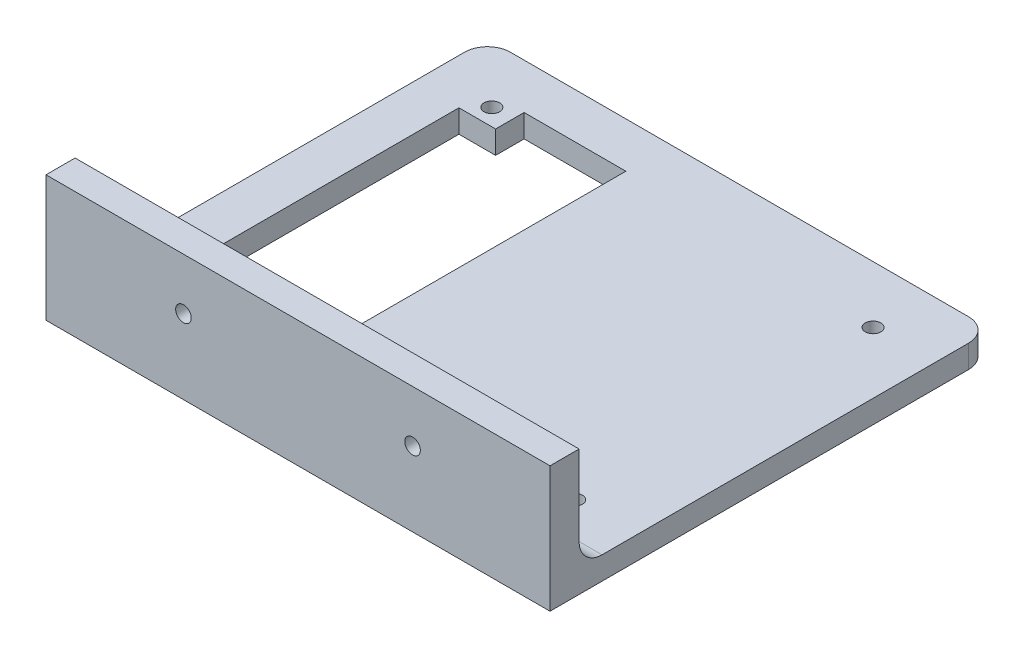
SolidWorks part; units mm, degrees
ref_plane "Front Plane" through (0, 0, 0) normal (0, 0, 1) x (1, 0, 0)
ref_plane "Top Plane" through (0, 0, 0) normal (0, 1, 0) x (1, 0, 0)
ref_plane "Right Plane" through (0, 0, 0) normal (1, 0, 0) x (0, 0, -1)
sketch "Sketch1" plane through (0, 0, 0) normal (0, 1, 0) x (1, 0, 0)
  line L1 (0, 0) -> (110, 0)
  line L2 (0, 0) -> (0, -90)
  line L3 (0, -90) -> (110, -90)
  line L4 (110, 0) -> (110, -90)
  dimension "D1" = 110
  dimension "D2" = 90
extrude "Boss-Extrude1" add sketch "Sketch1" along normal mid plane 5
sketch "Sketch3" plane through (0, 2.5, 0) normal (0, 1, 0) x (1, 0, 0)
  line L0 (55, 0) -> (55, -6.1118) construction
  line L1 (13.4, -77.5576) -> (96.6, -77.5576) construction
  line L2 (13.4, -77.5576) -> (13.4, -12.4424) construction
  line L3 (13.4, -12.4424) -> (96.6, -12.4424) construction
  line L4 (96.6, -77.5576) -> (96.6, -12.4424) construction
  line L5 (13.4, -77.5576) -> (96.6, -12.4424) construction
  line L6 (13.4, -12.4424) -> (96.6, -77.5576) construction
  line L7 (110, 0) -> (0, 0) construction
  line L8 (0, -45) -> (5.6534, -45) construction
  line L9 (0, 0) -> (0, -90) construction
  point P0 (55, -45)
  point P14 (96.6, -12.4424)
  point P15 (96.6, -77.5576)
  point P16 (13.4, -12.4424)
  point P17 (13.4, -77.5576)
  dimension "D1" = 83.2
  dimension "D2" = 65.1151
hole_wizard "M3 Clearance Hole1" positions "Sketch3" profile "Sketch4" hole size "M3" standard "ANSI Metric"
sketch "Sketch4" plane through (13.4, 2.5, 77.5576) normal (1, 0, 0) x (0, 0, 1)
  line L0 (0, 0) -> (0, 5)
  line L1 (0, 5) -> (1.7, 5)
  line L2 (1.7, 5) -> (1.7, 0)
  line L5 (1.7, 0) -> (0, 0)
  line L11 (0, -6.35) -> (0, 107.95) construction
  dimension "Thru Hole Dia." = 3.4
  dimension "Thru Hole Depth" = 5
sketch "Sketch5" plane through (0, 0, 0) normal (0, 1, 0) x (1, 0, 0)
  line L0 (110, -90) -> (110, 0) construction
  line L1 (0, -90) -> (110, -90)
  line L2 (0, -90) -> (0, -96.35)
  line L3 (0, -96.35) -> (110, -96.35)
  line L4 (110, -90) -> (110, -96.35)
  dimension "D1" = 6.35
extrude "Boss-Extrude2" add sketch "Sketch5" along normal blind 25 and the other way up to surface (2.5 mm away) other way up to face at (96.6, -2.5, 14.1424)
sketch "Sketch6" plane through (0, 0, 90) normal (0, 0, -1) x (-1, 0, 0)
  line L0 (0, 13.75) -> (-110, 13.75) construction
  line L1 (0, 2.5) -> (0, 25) construction
  line L2 (-110, 2.5) -> (-110, 25) construction
  line L3 (-55, 25) -> (-55, 2.5) construction
  line L4 (-110, 25) -> (0, 25) construction
  line L5 (-110, 2.5) -> (0, 2.5) construction
  point P12 (-30, 13.75)
  point P13 (-80, 13.75)
  dimension "D1" = 50
hole_wizard "CBORE for M3 SHCS1" positions "Sketch6" profile "Sketch7" counterbore size "M3" standard "ANSI Metric" end condition up to next
sketch "Sketch7" plane through (80, 13.75, 90) normal (1, 0, 0) x (0, 1, 0)
  line L0 (0, 0) -> (0, 6.35)
  line L1 (0, 6.35) -> (1.7, 6.35)
  line L3 (1.7, 6.35) -> (1.7, 3)
  line L4 (1.7, 3) -> (3.25, 3)
  line L5 (3.25, 3) -> (3.25, 0)
  line L7 (3.25, 0) -> (0, 0)
  line L11 (0, -6.35) -> (0, 107.95) construction
  dimension "Thru Hole Dia." = 3.4
  dimension "Thru Hole Depth" = 6.35
  dimension "C'Bore Dia." = 6.5
  dimension "C'Bore Depth" = 3
sketch "Sketch8" plane through (0, 2.5, 0) normal (0, 1, 0) x (1, 0, 0)
  line L0 (55, 0) -> (55, -10.0728) construction
  line L1 (9.9, -9.9) -> (100.1, -9.9) construction
  line L2 (9.9, -9.9) -> (9.9, -80.1) construction
  line L3 (9.9, -80.1) -> (100.1, -80.1) construction
  line L4 (100.1, -9.9) -> (100.1, -80.1) construction
  line L5 (9.9, -9.9) -> (100.1, -80.1) construction
  line L6 (9.9, -80.1) -> (100.1, -9.9) construction
  line L7 (110, 0) -> (0, 0) construction
  line L8 (0, -45) -> (9.6679, -45) construction
  line L9 (0, 0) -> (0, -90) construction
  line L10 (100.1, -16.1262) -> (92.1, -16.1262) construction
  line L11 (9.9, -9.9) -> (17.9, -9.9) construction
  line L12 (9.9, -9.9) -> (9.9, -16.1262) construction
  line L13 (9.9, -16.1262) -> (17.9, -16.1262) construction
  line L14 (17.9, -9.9) -> (17.9, -16.1262) construction
  line L15 (92.1, -9.9) -> (92.1, -16.1262) construction
  line L16 (92.1, -80.1) -> (92.1, -73.8738) construction
  line L17 (100.1, -73.8738) -> (92.1, -73.8738) construction
  line L18 (17.9, -80.1) -> (17.9, -73.8738) construction
  line L19 (9.9, -73.8738) -> (17.9, -73.8738) construction
  line L20 (17.9, -9.9) -> (92.1, -9.9)
  line L21 (92.1, -9.9) -> (92.1, -16.1262)
  line L22 (92.1, -16.1262) -> (100.1, -16.1262)
  line L23 (100.1, -16.1262) -> (100.1, -73.8738)
  line L24 (100.1, -73.8738) -> (92.1, -73.8738)
  line L25 (92.1, -73.8738) -> (92.1, -80.1)
  line L26 (92.1, -80.1) -> (17.9, -80.1)
  line L27 (17.9, -80.1) -> (17.9, -73.8738)
  line L28 (17.9, -73.8738) -> (9.9, -73.8738)
  line L29 (9.9, -73.8738) -> (9.9, -16.1262)
  line L30 (9.9, -16.1262) -> (17.9, -16.1262)
  line L31 (17.9, -16.1262) -> (17.9, -9.9)
  point P0 (55, -45)
  dimension "D1" = 90.2
  dimension "D2" = 70.2
  dimension "D3" = 8
extrude "Cut-Extrude1" cut sketch "Sketch8" against normal through all
sketch "Sketch9" plane through (0, 2.5, 0) normal (0, 1, 0) x (1, 0, 0)
  line L0 (17.9, -16.1262) -> (92.1, -73.8738) construction
  line L1 (92.1, -16.1262) -> (17.9, -73.8738) construction
  line L2 (17.9, -12.9583) -> (55, -41.8321)
  line L3 (17.9, -9.9) -> (17.9, -16.1262) construction
  line L4 (92.1, -73.8738) -> (100.1, -73.8738) construction
  line L5 (17.9, -12.9583) -> (17.9, -16.1262)
  line L6 (17.9, -16.1262) -> (13.8296, -16.1262)
  line L7 (17.9, -16.1262) -> (9.9, -16.1262) construction
  line L8 (13.8296, -16.1262) -> (50.9296, -45)
  line L9 (92.1, -80.1) -> (92.1, -73.8738) construction
  line L10 (92.1, -77.0417) -> (92.1, -73.8738)
  line L11 (92.1, -73.8738) -> (96.1704, -73.8738)
  line L12 (92.1, -12.9583) -> (55, -41.8321)
  line L13 (92.1, -16.1262) -> (92.1, -9.9) construction
  line L14 (9.9, -73.8738) -> (17.9, -73.8738) construction
  line L15 (96.1704, -16.1262) -> (59.0704, -45)
  line L16 (100.1, -16.1262) -> (92.1, -16.1262) construction
  line L17 (17.9, -73.8738) -> (17.9, -80.1) construction
  line L18 (17.9, -77.0417) -> (17.9, -73.8738)
  line L19 (17.9, -73.8738) -> (13.8296, -73.8738)
  line L20 (92.1, -12.9583) -> (92.1, -16.1262)
  line L21 (92.1, -16.1262) -> (96.1704, -16.1262)
  line L22 (59.0704, -45) -> (96.1704, -73.8738)
  line L23 (55, -48.1679) -> (92.1, -77.0417)
  line L24 (50.9296, -45) -> (13.8296, -73.8738)
  line L25 (55, -48.1679) -> (17.9, -77.0417)
  dimension "D1" = 2.5
  dimension "D2" = 2.5
  dimension "D3" = 2.5
  dimension "D4" = 2.5
extrude "Boss-Extrude3" [suppressed] add sketch "Sketch9" against normal through all
sketch "Sketch10" plane through (0, 2.5, 0) normal (0, 1, 0) x (1, 0, 0)
  line L0 (92.1, -9.9) -> (17.9, -9.9) construction
  line L1 (40.1, -9.9) -> (92.1, -9.9)
  line L2 (40.1, -9.9) -> (40.1, -80.1)
  line L3 (40.1, -80.1) -> (92.1, -80.1)
  line L4 (92.1, -9.9) -> (92.1, -16.1262)
  line L5 (92.1, -73.8738) -> (92.1, -80.1)
  line L6 (100.1, -16.1262) -> (92.1, -16.1262)
  line L7 (100.1, -16.1262) -> (100.1, -73.8738)
  line L8 (100.1, -73.8738) -> (92.1, -73.8738)
  dimension "D1" = 60
extrude "Boss-Extrude4" add sketch "Sketch10" against normal through all
fillet "Fillet1" radius 5 2 edges at (110, 0, 0) (0, 0, 0)
fillet "Fillet2" radius 5 1 edges at (55, 2.5, 90)
equation "\"D2@Sketch9\"=\"D1@Sketch9\""
equation "\"D3@Sketch9\"=\"D1@Sketch9\""
equation "\"D4@Sketch9\"=\"D1@Sketch9\""
